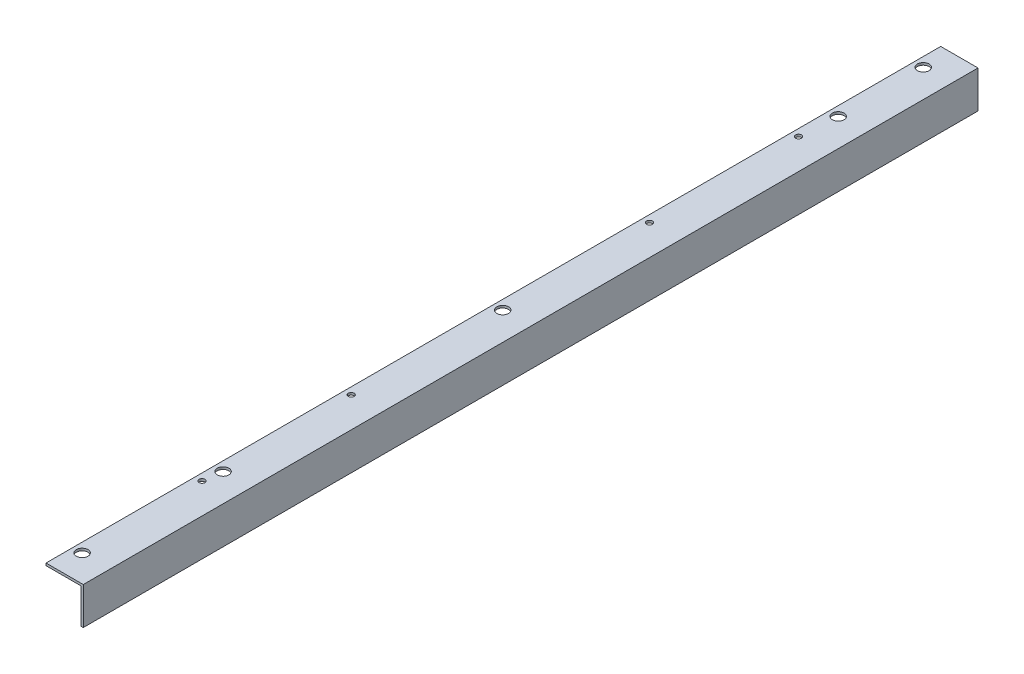
SolidWorks part; units mm, degrees
material "6063-T6"
ref_plane "Front Plane" through (0, 0, 0) normal (0, 0, 1) x (1, 0, 0)
ref_plane "Top Plane" through (0, 0, 0) normal (0, 1, 0) x (1, 0, 0)
ref_plane "Right Plane" through (0, 0, 0) normal (1, 0, 0) x (0, 0, -1)
sketch "Sketch1" plane through (0, 0, 0) normal (0, 0, 1) x (1, 0, 0)
  line L0 (0, 0) -> (-50.8, 0)
  line L1 (-50.8, 0) -> (-50.8, -3.175)
  line L2 (-50.8, -3.175) -> (-3.175, -3.175)
  line L3 (-3.175, -3.175) -> (-3.175, -50.8)
  line L4 (-3.175, -50.8) -> (0, -50.8)
  line L5 (0, -50.8) -> (0, 0)
  dimension "D1" = 50.8
  dimension "D2" = 3.175
extrude "Boss-Extrude1" add sketch "Sketch1" along normal blind 1219.2
sketch "Sketch2" plane through (0, 0, 0) normal (0, 1, 0) x (1, 0, 0)
  line L0 (0, 0) -> (-50.8, 0) construction
  line L1 (0, -1219.2) -> (0, 0) construction
  line L2 (0, -1219.2) -> (-50.8, -1219.2) construction
  circle A0 centre (-38.1, -36.5125) radius 7.9375
  circle A1 centre (-38.1, -1182.6875) radius 7.9375
  circle A2 centre (-38.1, -152.4) radius 7.9375
  circle A3 centre (-38.1, -609.6) radius 7.9375
  circle A4 centre (-38.1, -990.6) radius 7.9375
  dimension "D1" = 15.875
  dimension "D2" = 15.875
  dimension "D3" = 36.5125
  dimension "D4" = 38.1
  dimension "D5" = 36.5125
  dimension "D6" = 38.1
  dimension "D7" = 228.6
  dimension "D8" = 609.6
  dimension "D9" = 1066.8
extrude "Cut-Extrude1" cut sketch "Sketch2" against normal through all
extrude "Cut-Extrude3" cut sketch "Sketch4" against normal blind 44.45
sketch "Sketch4" plane through (-2.0299, 0, 893.1633) normal (0, 1, 0) x (1, 0, 0)
  circle A0 centre (-39.2451, 689.9633) radius 3.9687
pattern_linear "LPattern1" count 5 spacing 203.2 along (0, 0, 1) skipping (2, 0) of "Cut-Extrude3"
